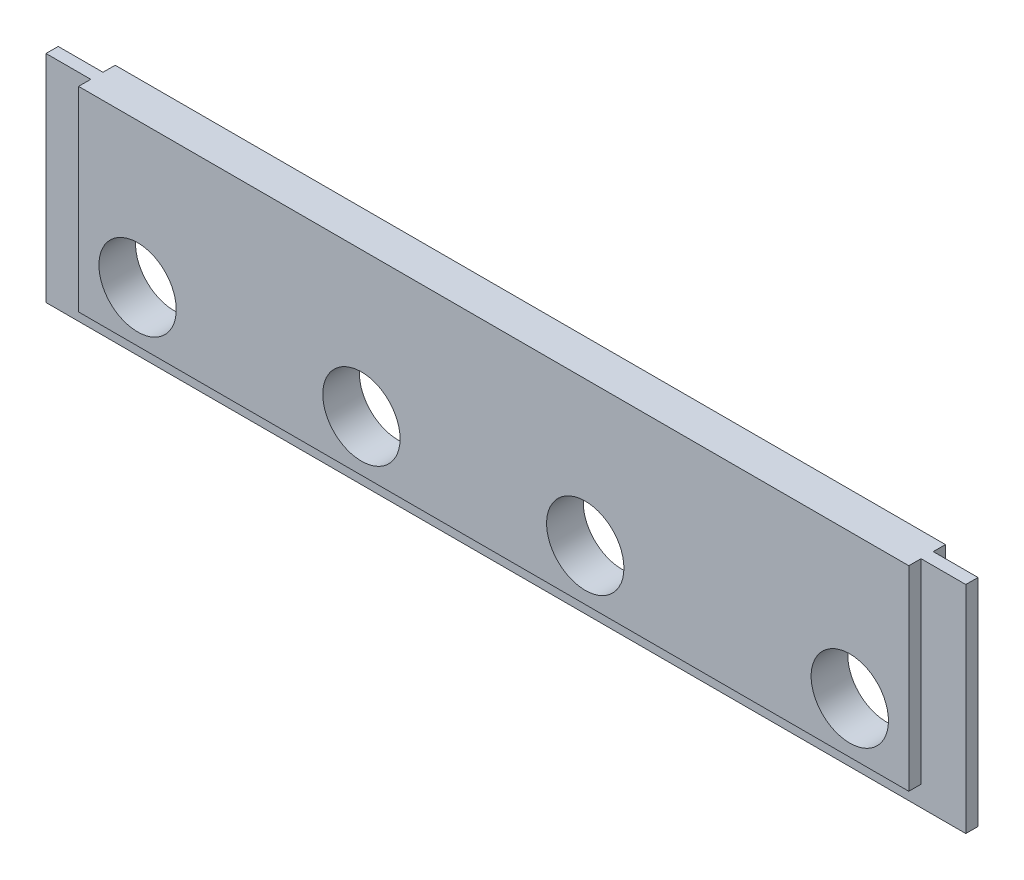
SolidWorks part; units mm, degrees
ref_plane "Front Plane" through (0, 0, 0) normal (0, 0, 1) x (1, 0, 0)
ref_plane "Top Plane" through (0, 0, 0) normal (0, 1, 0) x (1, 0, 0)
ref_plane "Right Plane" through (0, 0, 0) normal (1, 0, 0) x (0, 0, -1)
sketch "Sketch1" plane through (0, 0, 0) normal (0, 0, 1) x (1, 0, 0)
  line L0 (0, 1.4035) -> (0, -51.5965) construction
  line L1 (-113, -26.0198) -> (113, -26.0198)
  line L2 (-113, -26.0198) -> (-113, 26.9802)
  line L3 (-113, 26.9802) -> (113, 26.9802)
  line L4 (113, -26.0198) -> (113, 26.9802)
  point P0 (0, 0)
  dimension "D1" = 53
  dimension "D2" = 226
extrude "Boss-Extrude1" add sketch "Sketch1" along normal blind 9
sketch "Sketch3" plane through (0, 0, 9) normal (0, 0, 1) x (1, 0, 0)
  line L0 (0, 43.9546) -> (0, -51.4281) construction
  line L1 (-113, 26.9802) -> (-113, -26.0198) construction
  line L2 (-113, -26.0198) -> (113, -26.0198) construction
  line L3 (113, -26.0198) -> (113, 26.9802) construction
  circle A0 centre (-87.5, -8.5198) radius 9.5
  circle A1 centre (-32.5, -8.5198) radius 9.5
  circle A2 centre (22.5, -8.5198) radius 9.5
  circle A3 centre (87.5, -8.5198) radius 9.5
  dimension "D3" = 55
  dimension "D1" = 25.5
  dimension "D2" = 17.5
  dimension "D4" = 55
  dimension "D5" = 65
extrude "Cut-Extrude1" cut sketch "Sketch3" against normal blind 9
sketch "Sketch2" plane through (0, -26.0198, 0) normal (0, -1, 0) x (1, 0, 0)
  line L0 (0, -24.1939) -> (0, -33.1939) construction
  line L1 (-102, 9) -> (-102, 0)
  line L2 (-102, 9) -> (-113, 9)
  line L3 (-113, 9) -> (113, 9) construction
  line L4 (-113, 9) -> (-113, 0)
  line L5 (52.4605, 0) -> (-52.4605, 0) construction
  line L6 (-113, 9) -> (-113, 0) construction
  line L7 (-113, 0) -> (-102, 0)
  line L8 (-113, 6) -> (-102, 6)
  line L9 (-113, 3) -> (-102, 3)
  line L10 (113, 9) -> (113, 0) construction
  line L11 (0, 25.8471) -> (0, -17.451) construction
  line L12 (113, 3) -> (102, 3)
  line L13 (113, 6) -> (102, 6)
  line L14 (113, 0) -> (102, 0)
  line L15 (113, 9) -> (113, 0)
  line L16 (102, 9) -> (113, 9)
  line L17 (102, 9) -> (102, 0)
  line M6 (-113, 0) -> (113, 0)
  line M7 (113, 0) -> (113, 9)
  line M8 (113, 9) -> (-113, 9)
  line M9 (-113, 9) -> (-113, 0)
  dimension "D1" = 3
  dimension "D2" = 3
  dimension "D3" = 11
extrude "Cut-Extrude2" cut sketch "Sketch2" against normal through all contours L8 L1 M9 M8 | L9 L1 M9 M6 | L17 L13 M8 M7 | L12 L17 M6 M7
sketch "Sketch4" plane through (-113, 0, 0) normal (-1, 0, 0) x (0, 0, 1)
  line L0 (9, 26.9802) -> (9, -26.0198) construction
  line L1 (0, -26.0198) -> (9, -26.0198)
  line L2 (0, -26.0198) -> (0, -21.0198)
  line L3 (0, -21.0198) -> (9, -21.0198)
  line L4 (9, -26.0198) -> (9, -21.0198)
  line L5 (3, -23.1235) -> (3, -21.0198)
  line L6 (3, 26.9802) -> (3, -26.0198) construction
  line L7 (3, -21.0198) -> (3, -26.0198)
  line L8 (6, -21.0198) -> (6, -26.0198)
  line L9 (6, 26.9802) -> (6, -26.0198) construction
  line M2 (3, 26.9802) -> (3, -26.0198)
  line M4 (6, -26.0198) -> (6, 26.9802)
  dimension "D1" = 5
extrude "Cut-Extrude3" cut sketch "Sketch4" against normal through all contours L3 L2 L1 M2 | L1 L4 L3 M4
